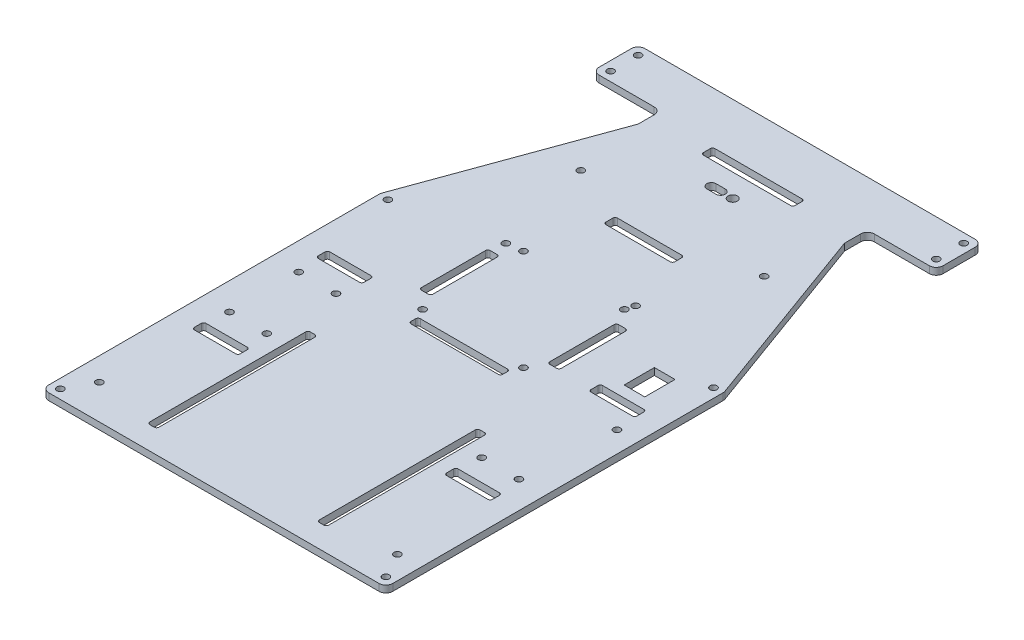
SolidWorks part; units mm, degrees
ref_plane "Front Plane" through (0, 0, 0) normal (0, 0, 1) x (1, 0, 0)
ref_plane "Top Plane" through (0, 0, 0) normal (0, 1, 0) x (1, 0, 0)
ref_plane "Right Plane" through (0, 0, 0) normal (1, 0, 0) x (0, 0, -1)
sketch "Sketch1" plane through (0, 0, 0) normal (0, 1, 0) x (1, 0, 0)
  line L0 (-72, 110) -> (-48, 110)
  line L1 (72, 130) -> (-72, 130)
  line L2 (75, 127) -> (75, 113)
  line L3 (72, -130) -> (-72, -130)
  line L4 (-75, 127) -> (-75, 113)
  line L5 (75, 130) -> (-75, -130) construction
  line L6 (75, -130) -> (-75, 130) construction
  line L7 (-45, 107) -> (-45, 100)
  line L8 (-45, 100) -> (-74.8191, 18.0728)
  line L9 (0, 0) -> (0, 130) construction
  line L10 (-75, 17.0467) -> (-75, -127)
  line L11 (45, 100) -> (74.8191, 18.0728)
  line L12 (45, 107) -> (45, 100)
  line L13 (72, 110) -> (48, 110)
  line L14 (75, 17.0467) -> (75, -127)
  line L15 (-75, 120) -> (75, 120) construction
  line L26 (-20, 95) -> (20, 95) construction
  line L28 (0, 0) -> (0, -130) construction
  line L35 (-21.5, -60) -> (21.5, -60) construction
  line L36 (-21.5, -38.5) -> (21.5, -38.5) construction
  line L37 (-21.5, -38.5) -> (-21.5, -81.5) construction
  line L38 (-21.5, -81.5) -> (21.5, -81.5) construction
  line L39 (21.5, -38.5) -> (21.5, -81.5) construction
  line L40 (-21.5, -38.5) -> (21.5, -81.5) construction
  line L41 (-21.5, -81.5) -> (21.5, -38.5) construction
  line L65 (19, 102.5) -> (-19, 102.5)
  line L66 (20, 103.5) -> (20, 106.5)
  line L67 (19, 107.5) -> (-19, 107.5)
  line L68 (-20, 103.5) -> (-20, 106.5)
  line L69 (20, 102.5) -> (-20, 107.5) construction
  line L70 (20, 107.5) -> (-20, 102.5) construction
  arc A0 (-72, -130) -> (-75, -127) centre (-72, -127) cw
  arc A1 (75, -127) -> (72, -130) centre (72, -127) cw
  arc A2 (74.8191, 18.0728) -> (75, 17.0467) centre (72, 17.0467) cw
  arc A3 (-74.8191, 18.0728) -> (-75, 17.0467) centre (-72, 17.0467) ccw
  arc A4 (-48, 110) -> (-45, 107) centre (-48, 107) cw
  arc A5 (45, 107) -> (48, 110) centre (48, 107) cw
  arc A6 (72, 130) -> (75, 127) centre (72, 127) cw
  arc A7 (72, 110) -> (75, 113) centre (72, 113) ccw
  arc A8 (-72, 130) -> (-75, 127) centre (-72, 127) ccw
  arc A9 (-72, 110) -> (-75, 113) centre (-72, 113) cw
  arc A40 (-19, 107.5) -> (-20, 106.5) centre (-19, 106.5) ccw
  arc A41 (-19, 102.5) -> (-20, 103.5) centre (-19, 103.5) cw
  arc A42 (19, 102.5) -> (20, 103.5) centre (19, 103.5) ccw
  arc A43 (20, 106.5) -> (19, 107.5) centre (19, 106.5) ccw
  circle A77 centre (-71, -126) radius 1.5
  circle A78 centre (-71, 16.8704) radius 1.5
  circle A80 centre (71, -126) radius 1.5
  circle A81 centre (71, 16.8704) radius 1.5
  circle A83 centre (-71, 126) radius 1.5
  circle A84 centre (-71, 114) radius 1.5
  circle A85 centre (71, 114) radius 1.5
  circle A86 centre (71, 126) radius 1.5
  point P0 (0, 0)
  point P24 (75, 17.5757)
  point P27 (-75, 17.5757)
  point P30 (-45, 110)
  point P33 (45, 110)
  point P39 (75, 110)
  point P45 (-75, 110)
  point P65 (0, 105)
  point P81 (0, 95)
  point P107 (0, -60)
  dimension "D7" = 3
  dimension "D8" = 4
  dimension "D9" = 4
  dimension "D14" = 81.9272
  dimension "D15" = 3
  dimension "D20" = 4
  dimension "D30" = 4
  dimension "D31" = 4
  dimension "D41" = 5
  dimension "D48" = 1
  dimension "D6" = 3
  dimension "D16" = 3
  dimension "D19" = 3
  dimension "D1" = 150
  dimension "D2" = 260
  dimension "D4" = 10
  dimension "D10" = 70
  dimension "D11" = 20
  dimension "D13" = 35
  dimension "D12" = 40
  dimension "D17" = 4
  dimension "D18" = 4
  dimension "D27" = 43
  dimension "D28" = 43
  dimension "D29" = 70
  dimension "D46" = 40
  dimension "D47" = 25
extrude "Boss-Extrude1" add sketch "Sketch1" along normal blind 3
sketch "Sketch2" plane through (0, 3, 0) normal (0, 1, 0) x (1, 0, 0)
  line L1 (65, -74.5) -> (45, -69.5) construction
  line L5 (65, -69.5) -> (45, -74.5) construction
  line L6 (0, -130) -> (0, 130) construction
  line L7 (-72, -130) -> (72, -130) construction
  line L8 (72, 130) -> (-72, 130) construction
  line L13 (0, 5) -> (25, 5) construction
  line L18 (75, -127) -> (75, 17.0467) construction
  line L19 (-25, 35) -> (25, 35) construction
  line L20 (-25, 35) -> (-25, -25) construction
  line L21 (-25, -25) -> (25, -25) construction
  line L26 (64, -11.5) -> (46, -11.5)
  line L27 (-65.625, -23.4) -> (-44.375, -23.4) construction
  line L28 (-65.625, -23.4) -> (-65.625, -66.6) construction
  line L29 (-65.625, -66.6) -> (-44.375, -66.6) construction
  line L30 (-44.375, -23.4) -> (-44.375, -66.6) construction
  line L31 (-65.625, -23.4) -> (-44.375, -66.6) construction
  line L32 (-65.625, -66.6) -> (-44.375, -23.4) construction
  line L33 (-55, -45) -> (-55, -66.6) construction
  line L34 (25, 35) -> (25, -25) construction
  line L35 (-25, 35) -> (25, -25) construction
  line L36 (-25, -25) -> (25, 35) construction
  line L41 (-55, -45) -> (-44.375, -45) construction
  line L42 (50.5, 11.6) -> (59.5, 11.6)
  line L43 (50.5, 11.6) -> (50.5, -1.6)
  line L44 (50.5, -1.6) -> (59.5, -1.6)
  line L45 (59.5, 11.6) -> (59.5, -1.6)
  line L46 (50.5, 11.6) -> (59.5, -1.6) construction
  line L47 (50.5, -1.6) -> (59.5, 11.6) construction
  line L48 (-64, -15.5) -> (-46, -15.5)
  line L49 (-65, -16.5) -> (-65, -19.5)
  line L50 (-64, -20.5) -> (-46, -20.5)
  line L51 (-45, -16.5) -> (-45, -19.5)
  line L52 (-65, -15.5) -> (-45, -20.5) construction
  line L53 (-65, -20.5) -> (-45, -15.5) construction
  line L54 (-65, -69.5) -> (-45, -74.5) construction
  line L55 (-65, -74.5) -> (-45, -69.5) construction
  line L56 (-45, -73.5) -> (-45, -70.5)
  line L57 (-64, -69.5) -> (-46, -69.5)
  line L58 (-65, -73.5) -> (-65, -70.5)
  line L59 (-64, -74.5) -> (-46, -74.5)
  line L60 (-39, -120) -> (-35, -50) construction
  line L61 (38, -50) -> (36, -50)
  line L62 (39, -51) -> (39, -119)
  line L63 (38, -120) -> (36, -120)
  line L64 (35, -51) -> (35, -119)
  line L65 (39, -50) -> (35, -120) construction
  line L66 (39, -120) -> (35, -50) construction
  line L67 (-39, -50) -> (-35, -120) construction
  line L68 (-35, -51) -> (-35, -119)
  line L69 (-38, -120) -> (-36, -120)
  line L70 (-39, -51) -> (-39, -119)
  line L71 (-38, -50) -> (-36, -50)
  line L72 (-5.5, 92.5) -> (-1.5, 92.5) construction
  line L73 (-5.5, 94.5) -> (-1.5, 94.5)
  line L74 (-5.5, 90.5) -> (-1.5, 90.5)
  line L75 (-19, 102.5) -> (19, 102.5) construction
  line L76 (65, -10.5) -> (65, -7.5)
  line L77 (-14, 60) -> (14, 60)
  line L78 (-15, 59) -> (-15, 56)
  line L79 (-14, 55) -> (14, 55)
  line L80 (15, 59) -> (15, 56)
  line L81 (-15, 60) -> (15, 55) construction
  line L82 (-15, 55) -> (15, 60) construction
  line L83 (29.5, -10) -> (26.5, -10)
  line L84 (30.5, -9) -> (30.5, 19)
  line L85 (29.5, 20) -> (26.5, 20)
  line L86 (25.5, -9) -> (25.5, 19)
  line L87 (30.5, -10) -> (25.5, 20) construction
  line L88 (30.5, 20) -> (25.5, -10) construction
  line L89 (-29.5, 20) -> (-26.5, 20)
  line L90 (-25.5, -9) -> (-25.5, 19)
  line L91 (-29.5, -10) -> (-26.5, -10)
  line L92 (-30.5, -9) -> (-30.5, 19)
  line L93 (55, -45) -> (44.375, -45) construction
  line L94 (-39, -105) -> (39, -105) construction
  line L95 (-39, -105) -> (-39, -65) construction
  line L96 (-39, -65) -> (39, -65) construction
  line L97 (39, -105) -> (39, -65) construction
  line L98 (-39, -105) -> (39, -65) construction
  line L99 (-39, -65) -> (39, -105) construction
  line L100 (55, -45) -> (55, -66.6) construction
  line L101 (65.625, -66.6) -> (44.375, -23.4) construction
  line L102 (65.625, -23.4) -> (44.375, -66.6) construction
  line L103 (44.375, -23.4) -> (44.375, -66.6) construction
  line L104 (65.625, -66.6) -> (44.375, -66.6) construction
  line L105 (65.625, -23.4) -> (65.625, -66.6) construction
  line L106 (65.625, -23.4) -> (44.375, -23.4) construction
  line L107 (64, -74.5) -> (46, -74.5)
  line L108 (65, -73.5) -> (65, -70.5)
  line L109 (64, -69.5) -> (46, -69.5)
  line L110 (45, -73.5) -> (45, -70.5)
  line L115 (64, -6.5) -> (46, -6.5)
  line L116 (45, -10.5) -> (45, -7.5)
  line L117 (65, -11.5) -> (45, -6.5) construction
  line L118 (65, -6.5) -> (45, -11.5) construction
  circle A12 centre (-46.875, -60.1) radius 1.5
  circle A13 centre (-63.125, -29.9) radius 1.5
  circle A14 centre (-63.125, -60.1) radius 1.5
  circle A15 centre (-46.875, -29.9) radius 1.5
  circle A20 centre (22, 27) radius 1.5
  circle A21 centre (22, -17) radius 1.5
  circle A22 centre (-22, -17) radius 1.5
  circle A23 centre (-22, 27) radius 1.5
  circle A24 centre (65, -115) radius 1.5
  circle A25 centre (-65, -115) radius 1.5
  arc A26 (-64, -15.5) -> (-65, -16.5) centre (-64, -16.5) ccw
  arc A27 (-65, -19.5) -> (-64, -20.5) centre (-64, -19.5) ccw
  arc A28 (-46, -20.5) -> (-45, -19.5) centre (-46, -19.5) ccw
  arc A29 (-46, -15.5) -> (-45, -16.5) centre (-46, -16.5) cw
  arc A30 (-46, -74.5) -> (-45, -73.5) centre (-46, -73.5) ccw
  arc A31 (-46, -69.5) -> (-45, -70.5) centre (-46, -70.5) cw
  arc A32 (-65, -70.5) -> (-64, -69.5) centre (-64, -70.5) cw
  arc A33 (-64, -74.5) -> (-65, -73.5) centre (-64, -73.5) cw
  arc A34 (36, -50) -> (35, -51) centre (36, -51) ccw
  arc A35 (36, -120) -> (35, -119) centre (36, -119) cw
  arc A36 (39, -119) -> (38, -120) centre (38, -119) cw
  arc A37 (38, -50) -> (39, -51) centre (38, -51) cw
  arc A38 (-38, -50) -> (-39, -51) centre (-38, -51) ccw
  arc A39 (-39, -119) -> (-38, -120) centre (-38, -119) ccw
  arc A40 (-36, -120) -> (-35, -119) centre (-36, -119) ccw
  arc A41 (-36, -50) -> (-35, -51) centre (-36, -51) cw
  circle A44 centre (3.75, 92.5) radius 2
  arc A45 (-5.5, 94.5) -> (-5.5, 90.5) centre (-5.5, 92.5) ccw
  arc A46 (-1.5, 90.5) -> (-1.5, 94.5) centre (-1.5, 92.5) ccw
  arc A47 (-14, 60) -> (-15, 59) centre (-14, 59) ccw
  arc A48 (-15, 56) -> (-14, 55) centre (-14, 56) ccw
  arc A49 (14, 55) -> (15, 56) centre (14, 56) ccw
  arc A50 (14, 60) -> (15, 59) centre (14, 59) cw
  arc A51 (30.5, 19) -> (29.5, 20) centre (29.5, 19) ccw
  arc A52 (26.5, 20) -> (25.5, 19) centre (26.5, 19) ccw
  arc A53 (26.5, -10) -> (25.5, -9) centre (26.5, -9) cw
  arc A54 (29.5, -10) -> (30.5, -9) centre (29.5, -9) ccw
  arc A55 (-26.5, 20) -> (-25.5, 19) centre (-26.5, 19) cw
  arc A56 (-26.5, -10) -> (-25.5, -9) centre (-26.5, -9) ccw
  arc A57 (-30.5, 19) -> (-29.5, 20) centre (-29.5, 19) cw
  arc A58 (-29.5, -10) -> (-30.5, -9) centre (-29.5, -9) cw
  arc A59 (64, -74.5) -> (65, -73.5) centre (64, -73.5) ccw
  arc A60 (65, -70.5) -> (64, -69.5) centre (64, -70.5) ccw
  arc A61 (46, -69.5) -> (45, -70.5) centre (46, -70.5) ccw
  arc A62 (46, -74.5) -> (45, -73.5) centre (46, -73.5) cw
  circle A68 centre (63.125, -60.1) radius 1.5
  circle A70 centre (46.875, -60.1) radius 1.5
  circle A71 centre (65.875, -20.1) radius 1.5
  arc A72 (64, -11.5) -> (65, -10.5) centre (64, -10.5) ccw
  arc A73 (65, -7.5) -> (64, -6.5) centre (64, -7.5) ccw
  arc A74 (46, -6.5) -> (45, -7.5) centre (46, -7.5) ccw
  arc A75 (46, -11.5) -> (45, -10.5) centre (46, -10.5) cw
  point P18 (0, 5)
  point P25 (-55, -18)
  point P28 (0, 5)
  point P40 (55, 5)
  point P108 (-55, -72)
  point P109 (37, -85)
  point P142 (-37, -85)
  point P147 (-3.5, 92.5)
  point P154 (0, 57.5)
  point P171 (28, 5)
  point P203 (0, -85)
  point P226 (55, -72)
  point P227 (55, -9)
  dimension "D8" = 5
  dimension "D9" = 85
  dimension "D15" = 3
  dimension "D16" = 3
  dimension "D13" = 3
  dimension "D10" = 3
  dimension "D12" = 15
  dimension "D22" = 3
  dimension "D31" = 1
  dimension "D36" = 1
  dimension "D37" = 4
  dimension "D38" = 2
  dimension "D46" = 1
  dimension "D50" = 1
  dimension "D53" = 3
  dimension "D55" = 40
  dimension "D57" = 58
  dimension "D4" = 55
  dimension "D5" = 43.2
  dimension "D6" = 60
  dimension "D7" = 50
  dimension "D11" = 21.25
  dimension "D14" = 30.2
  dimension "D17" = 16.25
  dimension "D18" = 6.5
  dimension "D19" = 10
  dimension "D20" = 5
  dimension "D21" = 20
  dimension "D23" = 22
  dimension "D24" = 22
  dimension "D25" = 9
  dimension "D26" = 13.2
  dimension "D27" = 20
  dimension "D28" = 135
  dimension "D29" = 27
  dimension "D30" = 55
  dimension "D32" = 4
  dimension "D33" = 70
  dimension "D34" = 45
  dimension "D35" = 38
  dimension "D39" = 3.5
  dimension "D40" = 3.75
  dimension "D41" = 10
  dimension "D42" = 4
  dimension "D43" = 5
  dimension "D44" = 30
  dimension "D45" = 45
  dimension "D47" = 5
  dimension "D48" = 30
  dimension "D49" = 28
  dimension "D51" = 40
  dimension "D52" = 78
  dimension "D54" = 19
  dimension "D56" = 2
  dimension "D59" = 45
extrude "Cut-Extrude1" cut sketch "Sketch2" against normal blind 4
sketch "Sketch3" plane through (0, 3, 0) normal (0, 1, 0) x (1, 0, 0)
  line L0 (0, 0) -> (0, -130) construction
  line L1 (-19, -21) -> (19, -21)
  line L2 (-20, -22) -> (-20, -24)
  line L3 (-19, -25) -> (19, -25)
  line L4 (20, -22) -> (20, -24)
  line L5 (-20, -21) -> (20, -25) construction
  line L6 (-20, -25) -> (20, -21) construction
  line L8 (0, 0) -> (0, 130) construction
  line L9 (72, 130) -> (-72, 130) construction
  line L10 (0, -1.65) -> (0, 1.65) construction
  arc A0 (-19, -21) -> (-20, -22) centre (-19, -22) ccw
  arc A1 (-20, -24) -> (-19, -25) centre (-19, -24) ccw
  arc A2 (19, -25) -> (20, -24) centre (19, -24) ccw
  arc A3 (19, -21) -> (20, -22) centre (19, -22) cw
  circle A4 centre (23.1, 30.81) radius 1.5
  circle A5 centre (-28.8, 26.11) radius 1.5
  circle A8 centre (22, -17) radius 1.5
  circle A9 centre (22, -17) radius 1.5 construction
  circle A10 centre (-40, 70) radius 1.5
  circle A11 centre (40, 70) radius 1.5
  point P0 (0, -23)
  dimension "D3" = 1
  dimension "D5" = 3
  dimension "D6" = 3
  dimension "D10" = 3
  dimension "D11" = 47.81
  dimension "D8" = 3
  dimension "D1" = 4
  dimension "D2" = 40
  dimension "D4" = 23
  dimension "D7" = 51.9
  dimension "D9" = 4.7
  dimension "D12" = 1.1
  dimension "D13" = 40
  dimension "D14" = 60
extrude "Cut-Extrude2" cut sketch "Sketch3" against normal blind 4
